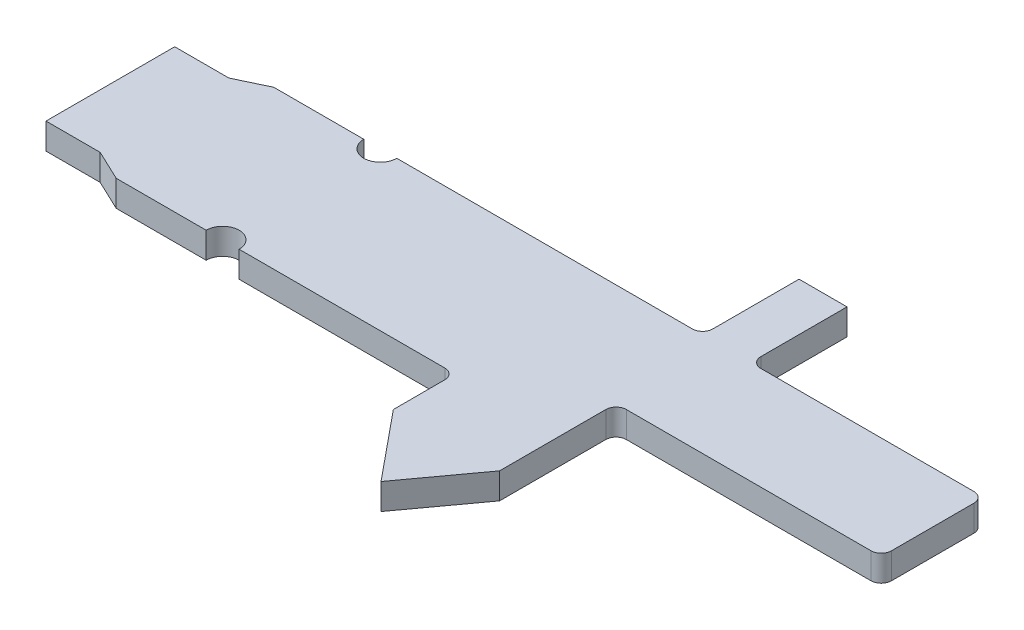
SolidWorks part; units mm, degrees
ref_plane "Front Plane" through (0, 0, 0) normal (0, 0, 1) x (1, 0, 0)
ref_plane "Top Plane" through (0, 0, 0) normal (0, 1, 0) x (1, 0, 0)
ref_plane "Right Plane" through (0, 0, 0) normal (1, 0, 0) x (0, 0, -1)
sketch "Sketch2" plane through (0, 0, 0) normal (0, 1, 0) x (1, 0, 0)
  line L0 (14.732, 2.54) -> (14.732, -0.508)
  line L1 (-14.732, -2.3853) -> (-14.732, 2.3853)
  line L2 (0, 0) -> (-14.732, 0) construction
  line L3 (0.5842, 2.921) -> (-7.0358, 2.921)
  line L4 (4.2995, 6.4957) -> (4.2995, 3.302)
  line L5 (-14.732, 2.921) -> (14.732, -2.921) construction
  line L6 (-14.732, -2.921) -> (14.732, 2.921) construction
  line L7 (14.351, -0.889) -> (5.2832, -0.889)
  line L8 (6.4585, 2.921) -> (14.351, 2.921)
  line L9 (6.0775, 3.302) -> (6.0775, 6.4957)
  line L10 (4.2995, 6.4957) -> (6.0775, 6.4957)
  line L11 (0.5842, -2.921) -> (-7.0358, -2.921)
  line L12 (0.5842, 2.921) -> (3.9185, 2.921)
  line L13 (-8.2589, -2.921) -> (-11.5943, -2.921)
  line L14 (-11.5943, -2.921) -> (-12.7236, -2.3853)
  line L15 (0.9652, -3.302) -> (0.9652, -5.207)
  line L16 (4.9022, -2.921) -> (4.9022, -5.207)
  line L17 (0.9652, -5.207) -> (3.048, -7.747)
  line L18 (4.9022, -2.921) -> (4.9022, -1.27)
  line L19 (4.9022, -5.207) -> (3.048, -7.747)
  line L20 (-12.7236, -2.3853) -> (-14.732, -2.3853)
  line L21 (-8.2589, 2.921) -> (-11.5943, 2.921)
  line L22 (-11.5943, 2.921) -> (-12.7236, 2.3853)
  line L23 (-12.7236, 2.3853) -> (-14.732, 2.3853)
  arc A0 (4.2995, 3.302) -> (3.9185, 2.921) centre (3.9185, 3.302) cw
  arc A2 (-7.0358, 2.921) -> (-8.2589, 2.921) centre (-7.6473, 2.921) cw
  arc A3 (0.5842, -2.921) -> (0.9652, -3.302) centre (0.5842, -3.302) cw
  arc A4 (4.9022, -1.27) -> (5.2832, -0.889) centre (5.2832, -1.27) cw
  arc A5 (14.351, -0.889) -> (14.732, -0.508) centre (14.351, -0.508) ccw
  arc A6 (14.732, 2.54) -> (14.351, 2.921) centre (14.351, 2.54) ccw
  arc A7 (6.0775, 3.302) -> (6.4585, 2.921) centre (6.4585, 3.302) ccw
  arc A8 (-7.0358, -2.921) -> (-8.2589, -2.921) centre (-7.6473, -2.921) ccw
  point P0 (0, 0)
  point P15 (3.048, -7.747)
  point P29 (0.9652, -2.921)
  point P32 (4.9022, -0.889)
  point P35 (14.732, -0.889)
  dimension "D5" = 0.381
  dimension "D1" = 29.464
  dimension "D2" = 5.842
  dimension "D3" = 3.81
  dimension "D4" = 9.8298
  dimension "D6" = 29.464
  dimension "D7" = 7.62
  dimension "D8" = 2.286
  dimension "D9" = 2.286
  dimension "D10" = 1.778
extrude "Boss-Extrude1" add sketch "Sketch2" along normal blind 0.9652
ref_plane "Plane1" through (0, 0.4826, 0) normal (0, 1, 0) x (1, 0, 0)
